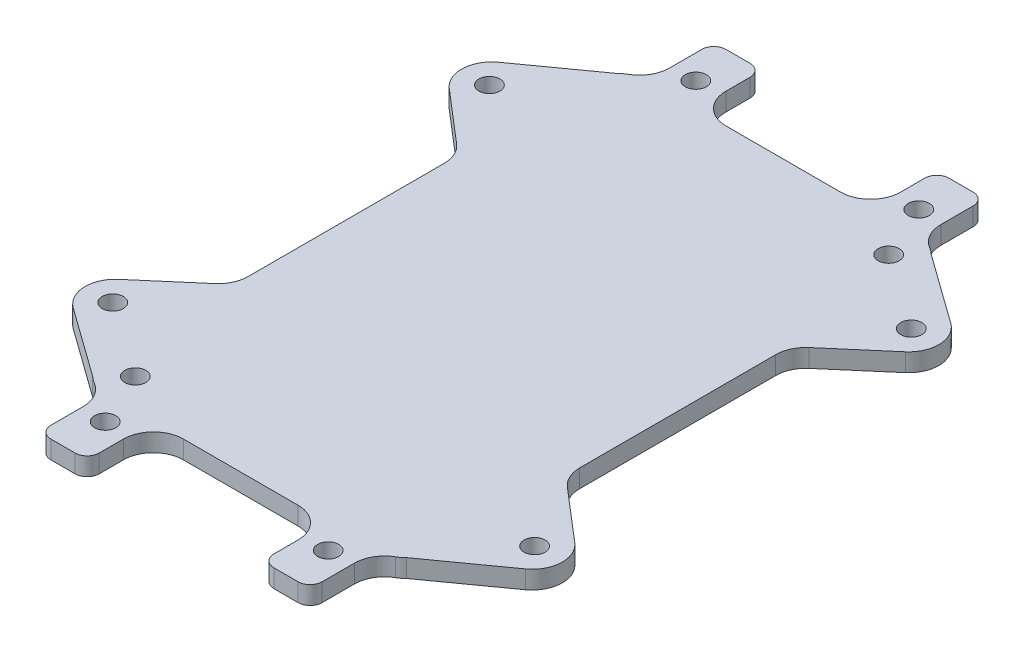
SolidWorks part; units mm, degrees
ref_plane "前视基准面" through (0, 0, 0) normal (0, 0, 1) x (1, 0, 0)
ref_plane "上视基准面" through (0, 0, 0) normal (0, 1, 0) x (1, 0, 0)
ref_plane "右视基准面" through (0, 0, 0) normal (1, 0, 0) x (0, 0, -1)
sketch "草图1" plane through (0, 0, 0) normal (0, 1, 0) x (1, 0, 0)
  line L0 (-26.0355, -43.5355) -> (-37.5121, -35.2939)
  line L1 (-22.5, -45) -> (22.5, -45)
  line L2 (-27.5, -40) -> (-27.5, 40)
  line L3 (-22.5, 45) -> (22.5, 45)
  line L4 (27.5, -40) -> (27.5, 40)
  line L5 (-27.5, -45) -> (27.5, 45) construction
  line L6 (-27.5, 45) -> (27.5, -45) construction
  line L7 (-37.8502, -27.4369) -> (-27.5, -18.5622)
  line L8 (0, 45) -> (0, -45) construction
  line L9 (26.0355, -43.5355) -> (37.5121, -35.2939)
  line L10 (37.8502, -27.4369) -> (27.5, -18.5622)
  line L11 (-27.5, 0) -> (27.5, 0) construction
  line L12 (26.0355, 43.5355) -> (37.5121, 35.2939)
  line L13 (37.8502, 27.4369) -> (27.5, 18.5622)
  line L14 (-26.0355, 43.5355) -> (-37.5121, 35.2939)
  line L15 (-37.8502, 27.4369) -> (-27.5, 18.5622)
  line L16 (-22.5, -45) -> (-22.5, -54)
  line L20 (-20.5, -56) -> (-16.5, -56)
  line L21 (-14.5, -54) -> (-14.5, -45)
  line L22 (22.5, -45) -> (22.5, -54)
  line L23 (20.5, -56) -> (16.5, -56)
  line L24 (14.5, -54) -> (14.5, -45)
  line L27 (14.5, 54) -> (14.5, 45)
  line L28 (20.5, 56) -> (16.5, 56)
  line L29 (22.5, 45) -> (22.5, 54)
  line L30 (-20.5, 56) -> (-16.5, 56)
  line L31 (-14.5, 54) -> (-14.5, 45)
  line L32 (-22.5, 45) -> (-22.5, 54)
  arc A0 (-37.5121, -35.2939) -> (-37.8502, -27.4369) centre (-34.5956, -31.2326) cw
  circle A1 centre (-35, -31.25) radius 1.75
  arc A2 (-27.5, 40) -> (-22.5, 45) centre (-22.5, 40) cw
  arc A3 (22.5, 45) -> (27.5, 40) centre (22.5, 40) cw
  arc A4 (22.5, -45) -> (27.5, -40) centre (22.5, -40) ccw
  arc A5 (-22.5, -45) -> (-27.5, -40) centre (-22.5, -40) cw
  circle A6 centre (35, -31.25) radius 1.75
  arc A7 (37.5121, -35.2939) -> (37.8502, -27.4369) centre (34.5956, -31.2326) ccw
  circle A8 centre (35, 31.25) radius 1.75
  arc A9 (37.5121, 35.2939) -> (37.8502, 27.4369) centre (34.5956, 31.2326) cw
  circle A10 centre (-35, 31.25) radius 1.75
  arc A11 (-37.5121, 35.2939) -> (-37.8502, 27.4369) centre (-34.5956, 31.2326) ccw
  arc A14 (16.5, -56) -> (14.5, -54) centre (16.5, -54) cw
  arc A16 (22.5, -54) -> (20.5, -56) centre (20.5, -54) cw
  arc A17 (-16.5, -56) -> (-14.5, -54) centre (-16.5, -54) ccw
  circle A18 centre (-22.5, -40) radius 1.75
  circle A20 centre (22.5, 40) radius 1.75
  arc A21 (-22.5, -54) -> (-20.5, -56) centre (-20.5, -54) ccw
  circle A22 centre (-18.5, -49) radius 1.75
  circle A23 centre (18.5, -49) radius 1.75
  arc A24 (16.5, 56) -> (14.5, 54) centre (16.5, 54) ccw
  arc A25 (22.5, 54) -> (20.5, 56) centre (20.5, 54) ccw
  circle A26 centre (18.5, 49) radius 1.75
  arc A27 (-22.5, 54) -> (-20.5, 56) centre (-20.5, 54) cw
  arc A28 (-16.5, 56) -> (-14.5, 54) centre (-16.5, 54) cw
  circle A29 centre (-18.5, 49) radius 1.75
  point P0 (0, 0)
  point P26 (-42.6829, -31.5806)
  point P59 (14.5, -56)
  point P62 (22.5, -56)
  point P65 (-14.5, -56)
  point P68 (-22.5, -56)
  dimension "D3" = 13.75
  dimension "D4" = 3.5
  dimension "D6" = 4.75
  dimension "D9" = 5
  dimension "D10" = 5
  dimension "D14" = 8
  dimension "D15" = 2
  dimension "D16" = 3.5
  dimension "D17" = 3.5
  dimension "D18" = 3.5
  dimension "D19" = 3.5
  dimension "D1" = 90
  dimension "D2" = 55
  dimension "D5" = 7.5
  dimension "D7" = 4.75
  dimension "D8" = 20
  dimension "D11" = 11
  dimension "D12" = 8
  dimension "D13" = 11
  dimension "D20" = 4
  dimension "D21" = 4
  dimension "D22" = 4
  dimension "D23" = 4
extrude "凸台-拉伸1" add sketch "草图1" along normal blind 3
fillet "圆角3" radius 5 12 edges at (27.5, 1.5, 18.5622) (27.5, 1.5, -18.5622) (-27.5, 1.5, 18.5622) (-27.5, 1.5, -18.5622) (-14.5, 1.5, 45) (-22.5, 1.5, 45) (22.5, 1.5, 45) (22.5, 1.5, -45) (-22.5, 1.5, -45) (-14.5, 1.5, -45) (14.5, 1.5, -45) (14.5, 1.5, 45)
